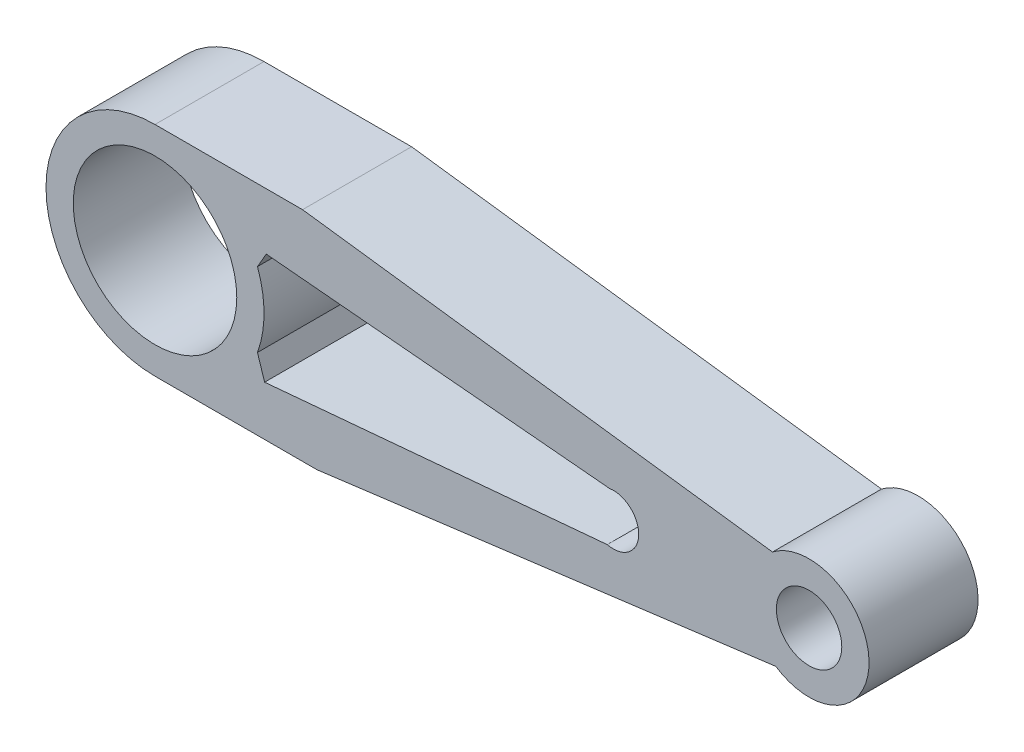
SolidWorks part; units mm, degrees
ref_plane "Płaszczyzna przednia" through (0, 0, 0) normal (0, 0, 1) x (1, 0, 0)
ref_plane "Płaszczyzna górna" through (0, 0, 0) normal (0, 1, 0) x (1, 0, 0)
ref_plane "Płaszczyzna prawa" through (0, 0, 0) normal (1, 0, 0) x (0, 0, -1)
sketch "Szkic1" [suppressed] plane through (0, 0, 0) normal (0, 0, 1) x (1, 0, 0)
  line L0 (-25, 0) -> (-25, 25)
  line L1 (-25, 0) -> (-25, -25)
  line L2 (-25, -25) -> (135, -25)
  line L3 (135, -25) -> (135, 25)
  line L4 (135, 25) -> (-25, 25)
  circle A0 centre (0, 0) radius 15
  circle A1 centre (120, 0) radius 6
  dimension "D2" = 30
  dimension "D3" = 12
  dimension "D1" = 120
  dimension "D4" = 50
  dimension "D5" = 160
  dimension "D6" = 25
  dimension "D7" = 25
extrude "Dodanie-wyciągnięcie1" [suppressed] add sketch "Szkic1" along normal blind 20
other "Grafika1"
other "Grafika (Zamknięta) -1"
sketch "Szkic2" plane through (0, 0, 0) normal (0, 0, 1) x (1, 0, 0)
  line L0 (0, -20) -> (29.7333, -20)
  line L1 (29.7333, -20) -> (113.9042, -9.1565)
  line L2 (0, 20) -> (27.0699, 20)
  line L3 (27.0699, 20) -> (113.2909, 8.7171)
  line L4 (20.4107, 9.6154) -> (18.8003, 6.8226)
  line L5 (20.4107, 9.6154) -> (83.3867, 3.8621)
  line L6 (20.1073, -10.8977) -> (18.8003, -6.8226)
  line L7 (20.1073, -10.8977) -> (82.9809, -5.2646)
  circle A0 centre (0, 0) radius 15
  circle A2 centre (120, 0) radius 6
  circle A4 centre (0, 0) radius 20
  circle A5 centre (120, 0) radius 11
  arc A6 (83.3867, 3.8621) -> (82.9809, -5.2646) centre (84.088, -0.7414) cw
  dimension "D2" = 30
  dimension "D3" = 12
  dimension "D4" = 22
  dimension "D5" = 40
  dimension "D11" = 4.6567
  dimension "D1" = 120
  dimension "D6" = 29.7333
  dimension "D7" = 84.171
  dimension "D8" = 27.0699
  dimension "D9" = 86.221
  dimension "D10" = 62.976
  dimension "D12" = 4.2795
  dimension "D13" = 3.2237
  dimension "D14" = 172.659
  dimension "D15" = 172.545
  dimension "D16" = 114.749
extrude "Dodanie-wyciągnięcie2" add sketch "Szkic2" along normal blind 20 contours L5 A6 L7 L6 A4 L0 L1 A5 L3 L2 L4 | A4 A0 | A5 A2
